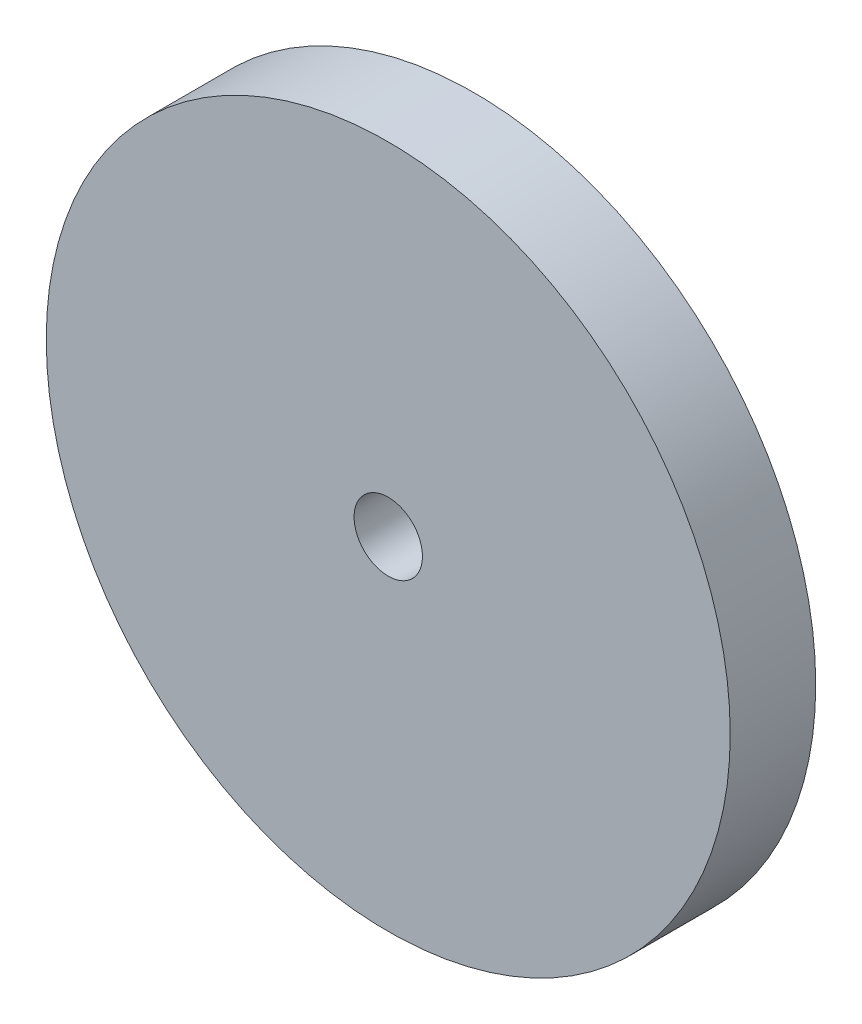
SolidWorks part; units mm, degrees
ref_plane "Front Plane" through (0, 0, 0) normal (0, 0, 1) x (1, 0, 0)
ref_plane "Top Plane" through (0, 0, 0) normal (0, 1, 0) x (1, 0, 0)
ref_plane "Right Plane" through (0, 0, 0) normal (1, 0, 0) x (0, 0, -1)
sketch "Sketch1" plane through (0, 0, 0) normal (0, 0, 1) x (1, 0, 0)
  circle A0 centre (0, 0) radius 12.7
  circle A1 centre (0, 0) radius 1.27
  dimension "D1" = 25.4
  dimension "D2" = 2.54
extrude "Boss-Extrude1" add sketch "Sketch1" along normal blind 3.175
